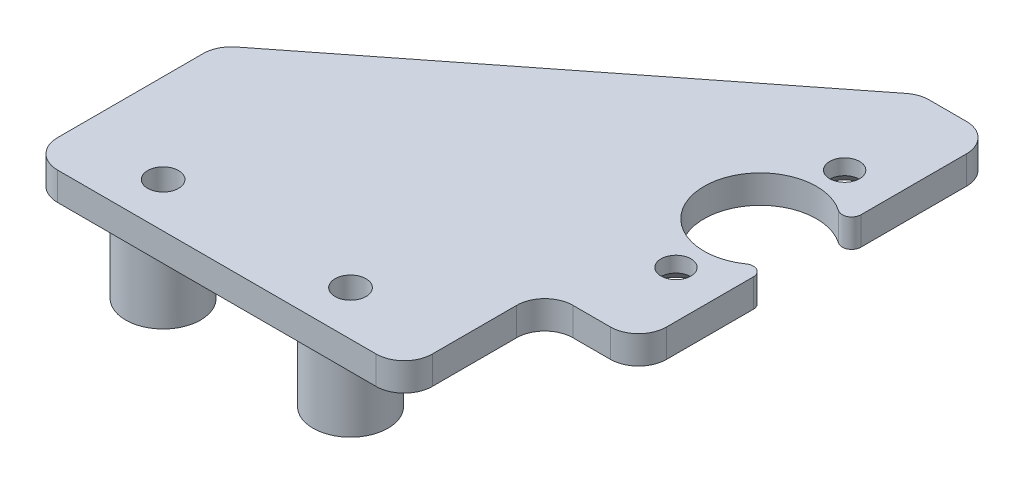
SolidWorks part; units mm, degrees
ref_plane "Plano frontal" through (0, 0, 0) normal (0, 0, 1) x (1, 0, 0)
ref_plane "Plano superior" through (0, 0, 0) normal (0, 1, 0) x (1, 0, 0)
ref_plane "Plano direito" through (0, 0, 0) normal (1, 0, 0) x (0, 0, -1)
sketch "Esboço1" plane through (0, 0, 0) normal (0, 1, 0) x (1, 0, 0)
  line L0 (0, 0) -> (25, 0) construction
  line L1 (0, 0) -> (0, 20) construction
  line L2 (-25, 20) -> (25, 20)
  line L5 (25, -20) -> (-25, -20)
  line L6 (-25, -20) -> (-25, 20)
  line L7 (25, 20) -> (25, -20)
  line L8 (25, 0.0001) -> (24.9995, 0.0001)
  line L9 (24.9995, -0.0001) -> (25, -0.0001)
  line L10 (24.9995, 0.0001) -> (24.9995, -0.0001)
  line L11 (25, -0.0001) -> (25, 0.0001)
  circle A0 centre (20, 9) radius 1.6
  circle A1 centre (20, -9) radius 1.6
  circle A2 centre (20, 0) radius 6
  point P3 (-25, 0)
  point P7 (0, 20)
  dimension "D4" = 3.2
  dimension "D6" = 12
  dimension "D1" = 50
  dimension "D2" = 40
  dimension "D3" = 0
  dimension "D5" = 18
  dimension "D7" = 5
  dimension "D8" = 5
extrude "Ressalto-extrusão10" add sketch "Esboço1" along normal blind 3 contours A2 L7 L2 L6 L5 A1 A0
fillet "Filete2" radius 1 2 edges at (25, 1.5, -3.3166) (25, 1.5, 3.3166)
chamfer "Chanfro1" distance 1.35 angle 45 2 edges at (20, 0, -7.4) (20, 0, 10.6)
sketch "Esboço5" plane through (0, 0, 0) normal (0, -1, 0) x (1, 0, 0)
  line L0 (-25, 20) -> (-25, 33)
  line L1 (-25, 33) -> (25, 33)
  line L2 (25, 33) -> (25, 20)
  line L3 (25, 20) -> (-25, 20)
  dimension "D1" = 13
extrude "Ressalto-extrusão13" add sketch "Esboço5" against normal blind 3
sketch "Esboço7" plane through (0, 0, 0) normal (0, -1, 0) x (1, 0, 0)
  line L0 (25, 5.7446) -> (25, 6.7446)
  line L1 (25, 5.7446) -> (25, 33) construction
  line L2 (25, 6.7446) -> (-25, 6.7446) construction
  line L3 (-25, 33) -> (-25, -20) construction
  line L4 (14, 0) -> (10, 0)
  circle A0 centre (-15.5, 28.2346) radius 1.65
  circle A1 centre (4.5, 28.2346) radius 1.65
  arc A2 (23.4286, 4.9239) -> (23.4286, -4.9239) centre (20, 0) ccw construction
  dimension "D2" = 3.3
  dimension "D1" = 1
  dimension "D3" = 20
  dimension "D4" = 4
  dimension "D5" = 21.49
  dimension "D6" = 21.49
  dimension "D7" = 5.5
extrude "Corte-extrusão1" cut sketch "Esboço7" against normal through all and the other way through all contours A0 | A1
sketch "Esboço8" plane through (0, 0, 0) normal (0, -1, 0) x (1, 0, 0)
  line L0 (-25, -20) -> (-25, 13)
  line L1 (-25, 33) -> (-25, -20) construction
  line L2 (-25, 13) -> (17, -20)
  line L3 (-25, -20) -> (25, -20) construction
  line L4 (17, -20) -> (-25, -20)
  line L5 (25, 33) -> (25, 18)
  line L6 (25, 5.7446) -> (25, 33) construction
  line L7 (25, 18) -> (15, 18)
  line L8 (15, 18) -> (15, 33)
  line L9 (25, 33) -> (-25, 33) construction
  line L10 (15, 33) -> (25, 33)
  dimension "D1" = 20
  dimension "D2" = 8
  dimension "D3" = 15
  dimension "D4" = 10
extrude "Corte-extrusão2" cut sketch "Esboço8" against normal through all contours L4 L0 L2 | L10 L5 L7 L8
fillet "Filete3" radius 3 7 edges at (25, 1.5, -20) (-25, 1.5, 33) (-25, 1.5, 13) (17, 1.5, -20) (15, 1.5, 18) (15, 1.5, 33) (25, 1.5, 18)
sketch "Esboço9" plane through (0, 0, 0) normal (0, -1, 0) x (1, 0, 0)
  line L0 (-15.5, 28.2346) -> (4.5, 28.2346) construction
  line L1 (-5.5, 28.2346) -> (-5.5, 10.2346) construction
  circle A0 centre (-15.5, 28.2346) radius 4
  circle A1 centre (4.5, 28.2346) radius 4
  circle A2 centre (-5.5, 10.2346) radius 4
  dimension "D1" = 8
  dimension "D2" = 18
extrude "Ressalto-extrusão14" add sketch "Esboço9" along normal blind 8
sketch "Esboço10" plane through (0, 0, 0) normal (0, -1, 0) x (1, 0, 0)
  circle A0 centre (-15.5, 28.2346) radius 1.65
  circle A1 centre (4.5, 28.2346) radius 1.65
  dimension "D1" = 3.3
extrude "Corte-extrusão5" cut sketch "Esboço10" along normal through all
